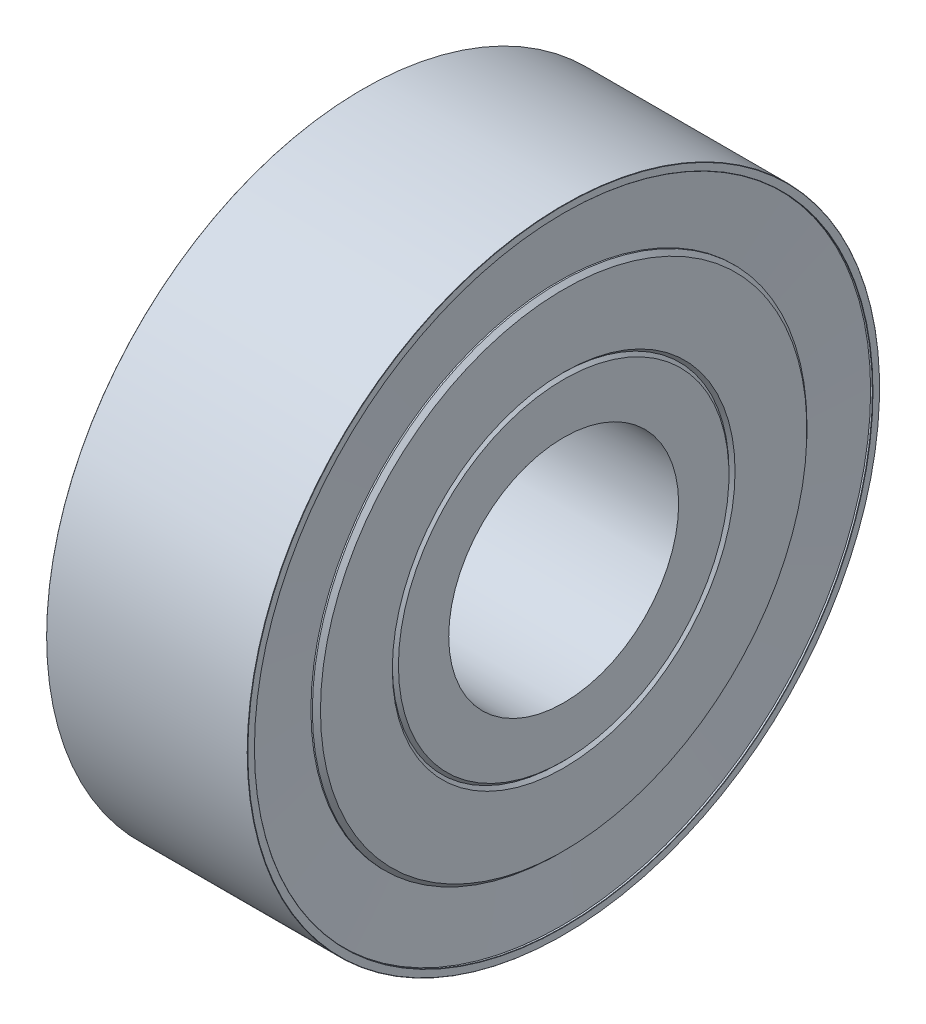
SolidWorks part; units mm, degrees
ref_plane "Front Plane" through (0, 0, 0) normal (0, 0, 1) x (1, 0, 0)
ref_plane "Top Plane" through (0, 0, 0) normal (0, 1, 0) x (1, 0, 0)
ref_plane "Right Plane" through (0, 0, 0) normal (1, 0, 0) x (0, 0, -1)
sketch "Sketch1" plane through (0, 0, 0) normal (0, 0, 1) x (1, 0, 0)
  line L0 (-3.5, 4) -> (3.5, 4)
  line L1 (-3.5, 5.75) -> (-3.3939, 5.8561)
  line L2 (-3.3939, 5.8561) -> (-3.5, 5.9621)
  line L4 (-3.5, 10.99) -> (-3.4892, 11)
  line L5 (-3.5, 10.99) -> (-3.5, 10.76)
  line L6 (-3.5, 5.9621) -> (-3.5, 8.4621)
  line L7 (-3.5, 8.4621) -> (-3.3586, 8.6036)
  line L8 (-3.3586, 8.6036) -> (-3.3086, 8.6036)
  line L9 (-3.4293, 10.75) -> (-3.3086, 8.6036)
  line L10 (-3.5, 10.99) -> (-3.5, 10.76)
  line L11 (-3.4293, 10.75) -> (-3.49, 10.75)
  line L12 (3.4892, 11) -> (-3.4892, 11)
  line L13 (-3.5, 5.75) -> (-3.5, 4)
  line L14 (-3.5, 10.76) -> (-3.49, 10.75)
  line L15 (3.5, 10.76) -> (3.49, 10.75)
  line L16 (3.5, 5.75) -> (3.5, 4)
  line L18 (3.4293, 10.75) -> (3.49, 10.75)
  line L19 (3.5, 10.99) -> (3.5, 10.76)
  line L20 (3.4293, 10.75) -> (3.3086, 8.6036)
  line L21 (3.3586, 8.6036) -> (3.3086, 8.6036)
  line L22 (3.5, 8.4621) -> (3.3586, 8.6036)
  line L23 (3.5, 5.9621) -> (3.5, 8.4621)
  line L24 (3.5, 10.99) -> (3.5, 10.76)
  line L25 (3.5, 10.99) -> (3.4892, 11)
  line L26 (3.3939, 5.8561) -> (3.5, 5.9621)
  line L27 (3.5, 5.75) -> (3.3939, 5.8561)
  line L29 (-0.5428, 0) -> (0.4017, 0)
revolve "Revolve1" add sketch "Sketch1" angle 360 about L29
